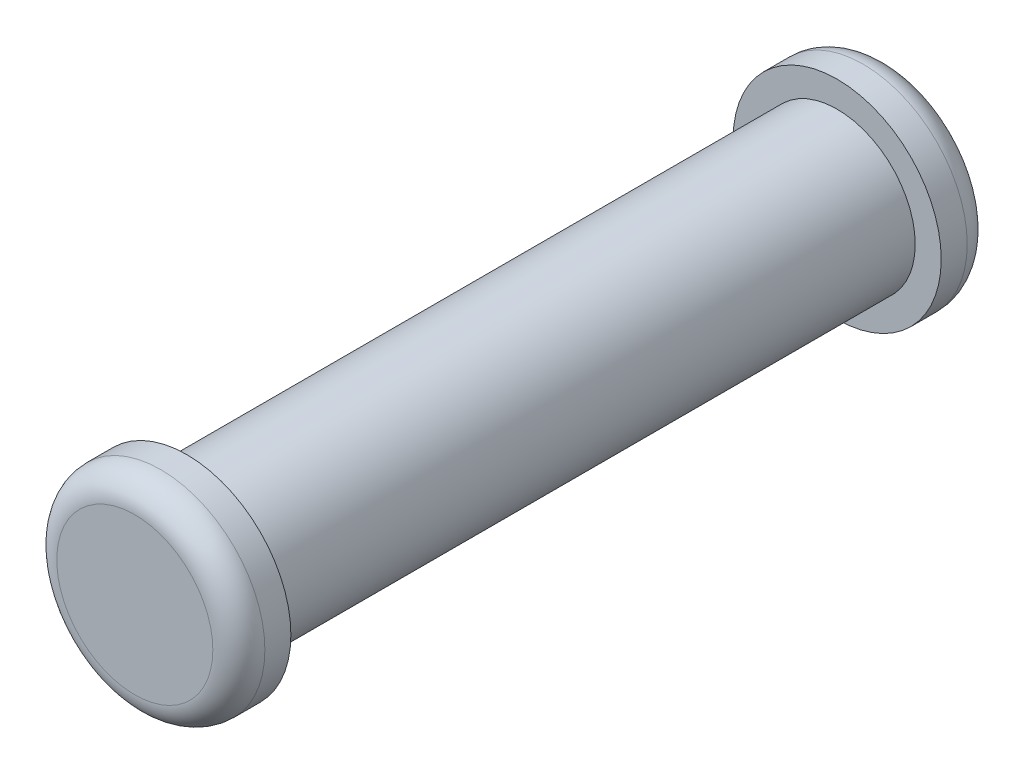
SolidWorks part; units mm, degrees
ref_plane "Front Plane" through (0, 0, 0) normal (0, 0, 1) x (1, 0, 0)
ref_plane "Top Plane" through (0, 0, 0) normal (0, 1, 0) x (1, 0, 0)
ref_plane "Right Plane" through (0, 0, 0) normal (1, 0, 0) x (0, 0, -1)
sketch "Sketch1" plane through (0, 0, 0) normal (0, 0, 1) x (1, 0, 0)
  circle A0 centre (0, 0) radius 1.5
  dimension "D1" = 3
extrude "Boss-Extrude1" add sketch "Sketch1" along normal blind 12.5
sketch "Sketch2" plane through (0, 0, 0) normal (0, 0, -1) x (-1, 0, 0)
  circle A0 centre (0, 0) radius 2
  dimension "D1" = 4
extrude "Boss-Extrude2" add sketch "Sketch2" along normal blind 1
sketch "Sketch3" plane through (0, 0, 12.5) normal (0, 0, 1) x (1, 0, 0)
  circle A1 centre (0, 0) radius 2
  circle A2 centre (0, 0) radius 2
  dimension "D1" = 0
extrude "Boss-Extrude3" add sketch "Sketch3" along normal blind 1
fillet "Fillet1" radius 0.5 2 edges at (-2, 0, -1) (2, 0, 13.5)
